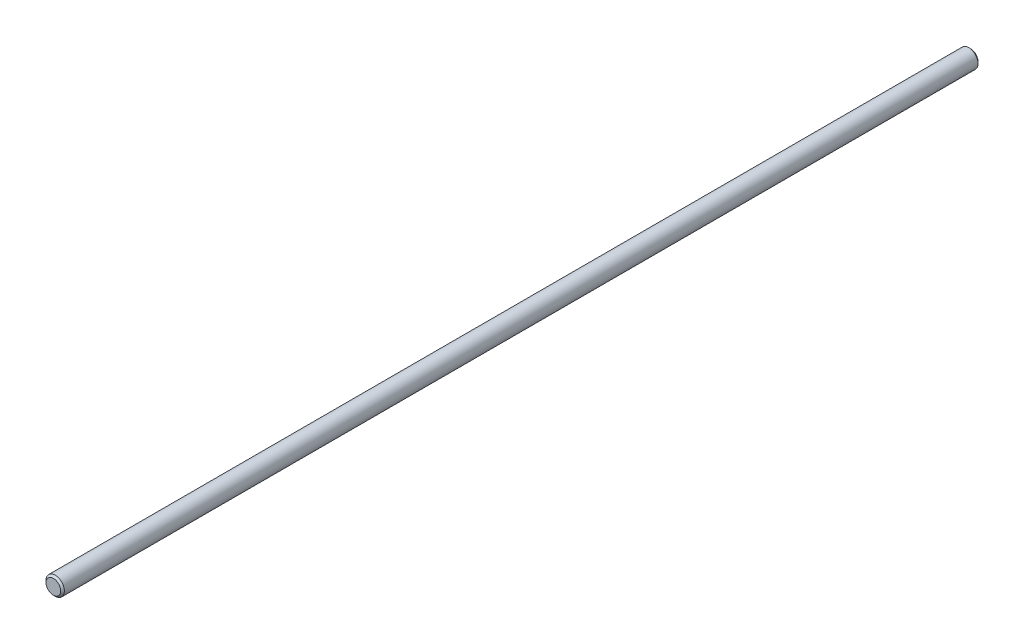
SolidWorks part; units mm, degrees
material "Cast Alloy Steel"
ref_plane "Front Plane" through (0, 0, 0) normal (0, 0, 1) x (1, 0, 0)
ref_plane "Top Plane" through (0, 0, 0) normal (0, 1, 0) x (1, 0, 0)
ref_plane "Right Plane" through (0, 0, 0) normal (1, 0, 0) x (0, 0, -1)
sketch "Sketch1" plane through (0, 0, 0) normal (0, 0, 1) x (1, 0, 0)
  circle A0 centre (0, 0) radius 10
  dimension "D1" = 20
extrude "Boss-Extrude1" add sketch "Sketch1" along normal blind 1000
chamfer "Chamfer1" distance 2 angle 45 2 edges at (10, 0, 0) (10, 0, 1000)
